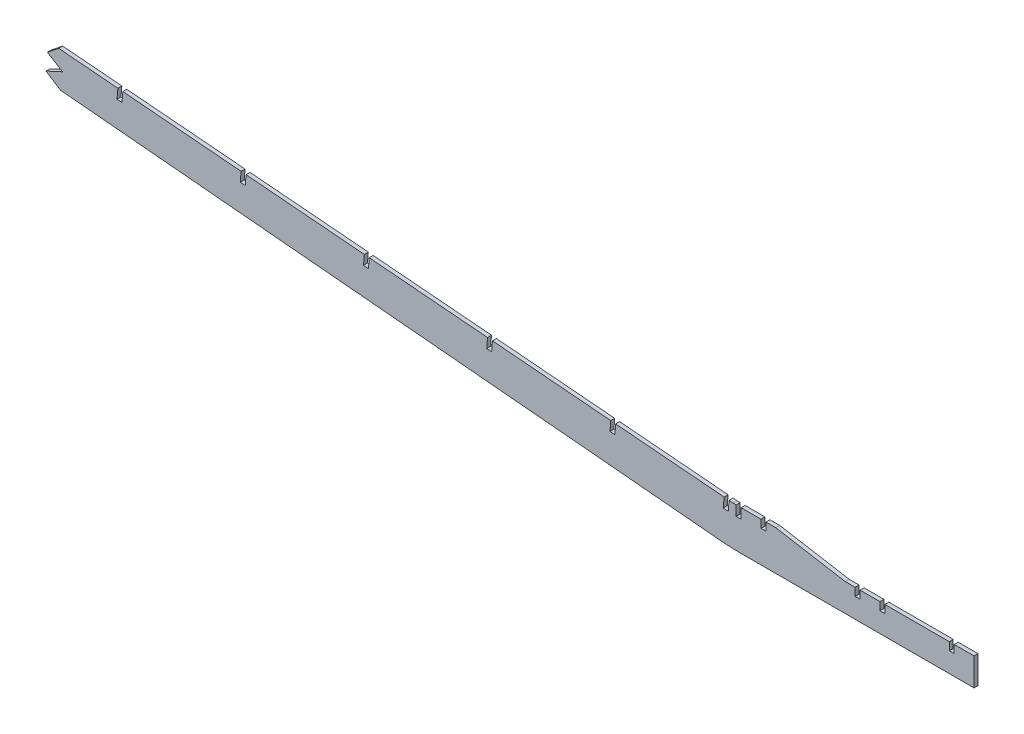
SolidWorks part; units mm, degrees
ref_plane "Front Plane" through (0, 0, 0) normal (0, 0, 1) x (1, 0, 0)
ref_plane "Top Plane" through (0, 0, 0) normal (0, 1, 0) x (1, 0, 0)
ref_plane "Right Plane" through (0, 0, 0) normal (1, 0, 0) x (0, 0, -1)
sketch "Sketch1" plane through (0, 0, 0) normal (0, 0, 1) x (1, 0, 0)
  line L0 (-949.6524, 80.0757) -> (-9.8872, -5.2596)
  line L1 (-945.9572, 86.1378) -> (-949.6524, 80.0757)
  line L8 (-6.7234, -5.5253) -> (-5.1293, 13.4579)
  line L9 (-5.1293, 13.4579) -> (-8.2932, 13.7235)
  line L10 (-8.2932, 13.7235) -> (-9.8872, -5.2596)
  line L11 (-9.8872, -5.2596) -> (-6.7234, -5.5253)
  line L12 (3.175, -5.8337) -> (3.175, 13.2163)
  line L13 (3.175, 13.2163) -> (0, 13.2163)
  line L14 (0, 13.2163) -> (0, -5.8337)
  line L15 (0, -5.8337) -> (3.175, -5.8337)
  line L17 (-943.1142, 119.9943) -> (-945.9572, 86.1378)
  line L18 (-945.9572, 86.1378) -> (-9.8872, -5.2596)
  line L19 (-6.7234, -5.5253) -> (0, -5.8337)
  line L20 (3.175, -5.8337) -> (152.4, -5.8337)
  line L21 (152.4, -5.8337) -> (152.4, 11.9463)
  line L22 (152.4, 11.9463) -> (69.85, 11.9463)
  line L23 (69.85, 11.9463) -> (25.4, 19.5663)
  line L24 (25.4, 19.5663) -> (-1.9861, 19.5663)
  line L25 (-1.9861, 19.5663) -> (-944.8986, 98.7448)
  line L26 (0, 13.2163) -> (0, 19.5663)
  line L27 (3.175, 13.2163) -> (3.175, 19.5663)
  line L28 (-5.1293, 13.4579) -> (-4.598, 19.7856)
  line L29 (-8.2932, 13.7235) -> (-7.7618, 20.0513)
  line L30 (-8.2932, 13.7235) -> (-945.4292, 92.426)
  line L31 (15.875, 19.5663) -> (15.875, 14.4863)
  line L32 (15.875, 14.4863) -> (19.05, 14.4863)
  line L33 (19.05, 14.4863) -> (19.05, 19.5663)
  line L34 (76.2, 6.8663) -> (76.2, 11.9463)
  line L35 (76.2, 6.8663) -> (79.375, 6.8663)
  line L36 (79.375, 6.8663) -> (79.375, 11.9463)
  line L37 (92.075, 11.9463) -> (92.075, 6.8663)
  line L38 (92.075, 6.8663) -> (95.25, 6.8663)
  line L39 (95.25, 6.8663) -> (95.25, 11.9463)
  line L40 (136.525, 11.9463) -> (136.525, 6.8663)
  line L41 (136.525, 6.8663) -> (139.7, 6.8663)
  line L42 (139.7, 6.8663) -> (139.7, 11.9463)
  line L44 (-949.6524, 80.0757) -> (-949.1211, 86.4035)
  line L45 (-949.1211, 86.4035) -> (-945.959, 86.1163)
  dimension "D1" = 25.4
  dimension "D2" = 6.35
extrude "Boss-Extrude1" add sketch "Sketch1" along normal blind 2.54
sketch "Sketch2" plane through (0, 0, 2.54) normal (0, 0, 1) x (1, 0, 0)
  line L1 (-76.483, 72.8473) -> (-82.5095, 1.0799)
  line L3 (-155.6446, 77.1971) -> (-161.4339, 8.255)
  line L5 (-234.8005, 81.6162) -> (-240.3617, 15.3891)
  line L7 (-313.9625, 85.9617) -> (-319.2865, 22.5591)
  line L9 (-393.1191, 90.3714) -> (-398.2146, 29.6908)
  line L11 (-472.2837, 94.686) -> (-477.1388, 36.8682)
  line L13 (-551.4418, 99.0783) -> (-556.0668, 44.0001)
  line L15 (-630.6082, 103.3716) -> (-634.991, 51.1773)
  line L17 (-709.7674, 107.7507) -> (-713.9195, 58.3043)
  line L19 (-788.9364, 112.0121) -> (-792.8436, 65.483)
  line L21 (-868.0976, 116.3681) -> (-871.7723, 72.6069)
  line L23 (-73.3191, 72.5816) -> (-79.3456, 0.8143)
  line L25 (-152.4808, 76.9314) -> (-158.27, 7.9893)
  line L27 (-231.6366, 81.3506) -> (-237.1978, 15.1234)
  line L29 (-310.7986, 85.696) -> (-316.1227, 22.2934)
  line L31 (-389.9552, 90.1057) -> (-395.0507, 29.4251)
  line L33 (-469.1198, 94.4203) -> (-473.9749, 36.6025)
  line L35 (-548.2779, 98.8126) -> (-552.903, 43.7344)
  line L37 (-627.4443, 103.1059) -> (-631.8272, 50.9116)
  line L39 (-706.6035, 107.485) -> (-710.7556, 58.0386)
  line L41 (-785.7726, 111.7464) -> (-789.6797, 65.2173)
  line L43 (-864.9337, 116.1024) -> (-868.6084, 72.3413)
  line L45 (-8.2932, 13.7235) -> (-945.4292, 92.426)
  line L47 (-7.7618, 20.0513) -> (-944.8986, 98.7448)
  line M27 (-7.7618, 20.0513) -> (-944.8986, 98.7448)
extrude "Cut-Extrude1" cut sketch "Sketch2" against normal through all and the other way through all contours L45 L43 L21 M27 | L45 L41 L19 M27 | L45 L39 L17 M27 | L45 L37 L15 M27 | L45 L35 L13 M27 | L45 L33 L11 M27 | L45 L31 L9 M27 | L45 L29 L7 M27 | L45 L27 L5 M27 | L45 L25 L3 M27 | L45 L23 L1 M27
sketch "Sketch3" plane through (0, 0, 2.54) normal (0, 0, 1) x (1, 0, 0)
  line L0 (-434.1875, 55.8592) -> (-441.4445, 50.0741)
  line L1 (-396.2844, 52.6764) -> (-472.0906, 59.042) construction
  line L2 (-441.4445, 50.0741) -> (-431.803, 44.0226)
  line L3 (-431.803, 44.0226) -> (-442.3497, 39.1715)
  line L4 (-442.3497, 39.1715) -> (-433.0143, 33.1624)
  line L5 (-949.6524, 80.0757) -> (-9.8872, -5.2596) construction
  line L6 (-434.1875, 55.8592) -> (-979.2227, 133.8808)
  line L7 (-979.2227, 133.8808) -> (-1000.0741, -11.7803)
  line L8 (-1000.0741, -11.7803) -> (-433.0143, 33.1624)
extrude "Cut-Extrude2" cut sketch "Sketch3" against normal blind 7.62 contours L8 L4 L3 L2 L0 L6 L7
